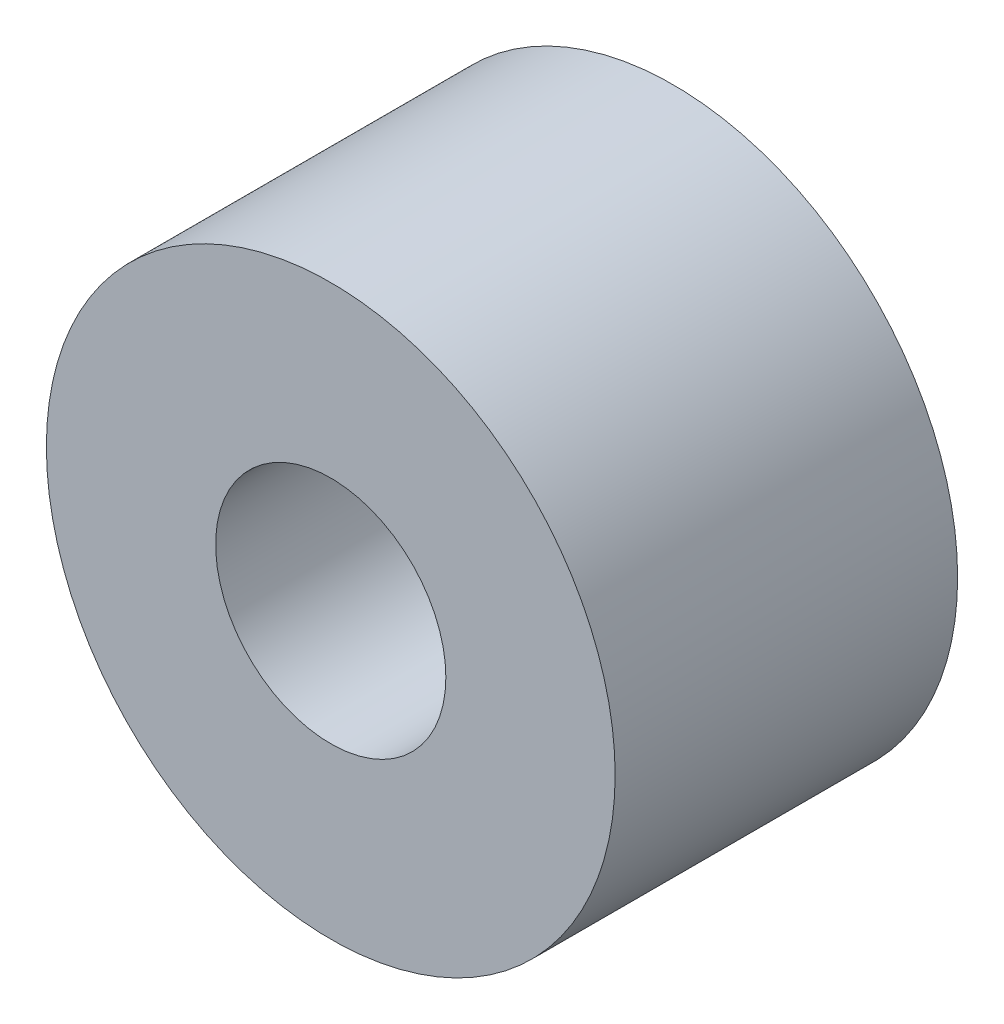
SolidWorks part; units mm, degrees
ref_plane "Front Plane" through (0, 0, 0) normal (0, 0, 1) x (1, 0, 0)
ref_plane "Top Plane" through (0, 0, 0) normal (0, 1, 0) x (1, 0, 0)
ref_plane "Right Plane" through (0, 0, 0) normal (1, 0, 0) x (0, 0, -1)
sketch "Sketch1" plane through (0, 0, 0) normal (0, 1, 0) x (1, 0, 0)
  line L0 (2.125, -3.75) -> (5.25, -3.75)
  line L1 (5.25, -3.75) -> (5.25, 0)
  line L2 (5.25, 0) -> (2.125, 0)
  line L3 (2.125, 0) -> (2.125, -3.75)
  line L4 (0, 0) -> (0, -3.75) construction
  dimension "D1" = 2.125
  dimension "D2" = 5.25
  dimension "D3" = 3.75
revolve "Revolve1" add sketch "Sketch1" angle 360 about L4
sketch "Sketch2" plane through (0, 0, 3.75) normal (0, 0, 1) x (1, 0, 0)
  circle A0 centre (0, 0) radius 2.125
  circle A1 centre (0, 0) radius 5.25
  dimension "D1" = 4.25
  dimension "D2" = 10.5
extrude "Boss-Extrude1" add sketch "Sketch2" along normal blind 3.0725
sketch "Sketch3" plane through (0, 0, 0) normal (0, 0, -1) x (-1, 0, 0)
  circle A0 centre (0, 0) radius 3
  circle A1 centre (0, 0) radius 5.25
  circle A2 centre (0, 0) radius 5.25
  dimension "D2" = 6
  dimension "D1" = 0
extrude "Cut-Extrude1" cut sketch "Sketch3" against normal blind 0.5
